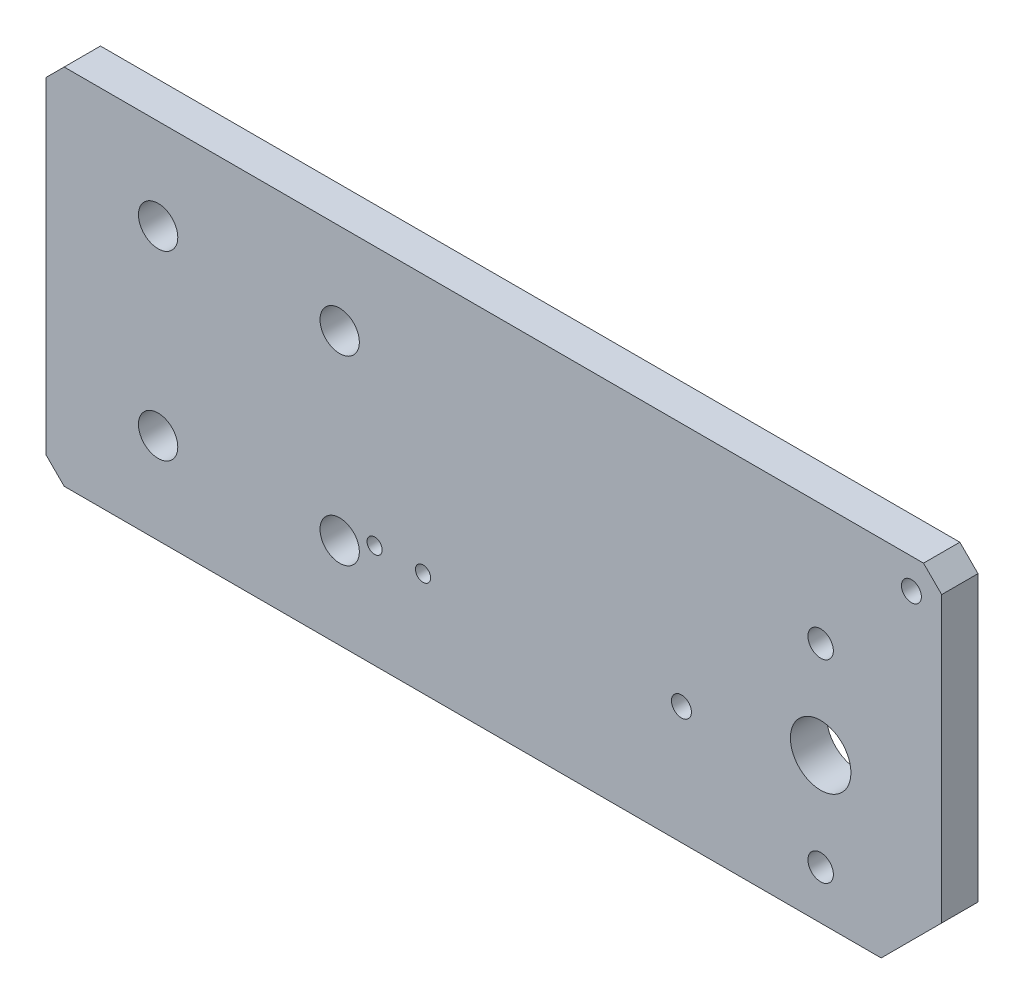
SolidWorks part; units mm, degrees
ref_plane "Front Plane" through (0, 0, 0) normal (0, 0, 1) x (1, 0, 0)
ref_plane "Top Plane" through (0, 0, 0) normal (0, 1, 0) x (1, 0, 0)
ref_plane "Right Plane" through (0, 0, 0) normal (1, 0, 0) x (0, 0, -1)
sketch "Sketch1" plane through (0, 0, 0) normal (0, 0, 1) x (1, 0, 0)
  line L1 (-53.5188, 27.4006) -> (94.4812, 27.4006)
  line L2 (-53.5188, 27.4006) -> (-53.5188, -32.5994)
  line L3 (-53.5188, -32.5994) -> (94.4812, -32.5994)
  line L4 (94.4812, 27.4006) -> (94.4812, -32.5994)
  circle A0 centre (-34.993, 12.4006) radius 3.25
  circle A1 centre (-4.993, 12.4006) radius 3.25
  circle A2 centre (-34.993, -17.5994) radius 3.25
  circle A3 centre (-4.993, -17.5994) radius 3.25
  circle A4 centre (74.4812, -8.5994) radius 5
  dimension "D4" = 30
  dimension "D5" = 30
  dimension "D6" = 6.5
  dimension "D7" = 10
  dimension "D8" = 20
  dimension "D9" = 24
  dimension "D1" = 148
  dimension "D2" = 60
  dimension "D3" = 45
extrude "Boss-Extrude1" add sketch "Sketch1" along normal blind 6
hole_wizard "M5x0.8 Tapped Hole1" positions "Sketch2" profile "Sketch3" tap size "M5x0.8" standard "ANSI Metric" end condition through all
sketch "Sketch2" plane through (0, 0, 6) normal (0, 0, 1) x (1, 0, 0)
  line L0 (94.4812, -32.5994) -> (94.4812, 27.4006) construction
  line L1 (-53.5188, -32.5994) -> (94.4812, -32.5994) construction
  point P0 (74.4812, 7.4006)
  point P2 (74.4812, -24.5994)
  dimension "D1" = 32
  dimension "D2" = 20
  dimension "D3" = 20
  dimension "D4" = 8
sketch "Sketch3" plane through (74.4812, 7.4006, 6) normal (1, 0, 0) x (0, -1, 0)
  line L0 (0, 0) -> (0, 6)
  line L1 (0, 6) -> (2.1, 6)
  line L2 (2.1, 6) -> (2.1, 0)
  line L5 (2.1, 0) -> (0, 0)
  line L11 (0, -6.35) -> (0, 107.95) construction
  dimension "Thru Tap Drill Dia." = 4.2
  dimension "Thru Tap Drill Depth" = 6
cosmetic thread "Hole Thread1"
cosmetic thread "Hole Thread2"
hole_wizard "M4x0.7 Tapped Hole1" positions "Sketch4" profile "Sketch5" tap size "M4x0.7" standard "ANSI Metric" end condition through all
sketch "Sketch4" plane through (0, 0, 6) normal (0, 0, 1) x (1, 0, 0)
  line L0 (-53.5188, -32.5994) -> (94.4812, -32.5994) construction
  line L1 (94.4812, -32.5994) -> (94.4812, 27.4006) construction
  line L2 (-53.5188, 27.4006) -> (-53.5188, -32.5994) construction
  point P0 (89.4812, 22.4006)
  point P2 (51.4812, -13.0994)
  dimension "D1" = 55
  dimension "D2" = 5
  dimension "D3" = 105
  dimension "D4" = 19.5
sketch "Sketch5" plane through (89.4812, 22.4006, 6) normal (1, 0, 0) x (0, -1, 0)
  line L0 (0, 0) -> (0, 6)
  line L1 (0, 6) -> (1.65, 6)
  line L2 (1.65, 6) -> (1.65, 0)
  line L5 (1.65, 0) -> (0, 0)
  line L11 (0, -6.35) -> (0, 107.95) construction
  dimension "Thru Tap Drill Dia." = 3.3
  dimension "Thru Tap Drill Depth" = 6
cosmetic thread "Hole Thread3"
cosmetic thread "Hole Thread4"
hole_wizard "M3x0.5 Tapped Hole1" positions "Sketch6" profile "Sketch7" tap size "M3x0.5" standard "ANSI Metric" end condition through all
sketch "Sketch6" plane through (0, 0, 6) normal (0, 0, 1) x (1, 0, 0)
  line L0 (-53.5188, 27.4006) -> (-53.5188, -32.5994) construction
  line L1 (-53.5188, -32.5994) -> (94.4812, -32.5994) construction
  point P0 (0.7812, -15.4494)
  point P2 (8.7812, -15.4494)
  dimension "D1" = 54.3
  dimension "D2" = 62.3
  dimension "D3" = 17.15
  dimension "D4" = 17.15
sketch "Sketch7" plane through (0.7812, -15.4494, 6) normal (1, 0, 0) x (0, -1, 0)
  line L0 (0, 0) -> (0, 6)
  line L1 (0, 6) -> (1.25, 6)
  line L2 (1.25, 6) -> (1.25, 0)
  line L5 (1.25, 0) -> (0, 0)
  line L11 (0, -6.35) -> (0, 107.95) construction
  dimension "Thru Tap Drill Dia." = 2.5
  dimension "Thru Tap Drill Depth" = 6
cosmetic thread "Hole Thread5"
cosmetic thread "Hole Thread6"
chamfer "Chamfer1" distance 10 angle 45 1 edges at (94.4812, -32.5994, 3)
chamfer "Chamfer2" distance 3 angle 45 3 edges at (94.4812, 27.4006, 3) (-53.5188, -32.5994, 3) (-53.5188, 27.4006, 3)
